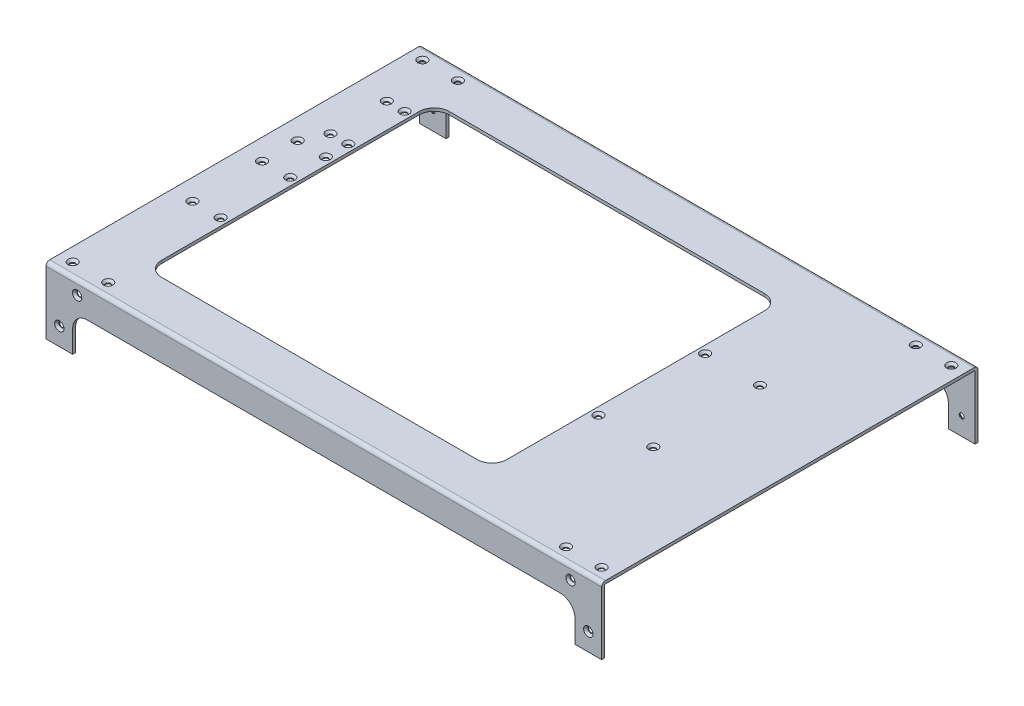
SolidWorks part; units mm, degrees
material "6061-T6 (SS)"
ref_plane "Front Plane" through (0, 0, 0) normal (0, 0, 1) x (1, 0, 0)
ref_plane "Top Plane" through (0, 0, 0) normal (0, 1, 0) x (1, 0, 0)
ref_plane "Right Plane" through (0, 0, 0) normal (1, 0, 0) x (0, 0, -1)
sketch "Sketch1" plane through (0, 0, 0) normal (1, 0, 0) x (0, 0, -1)
  line L0 (125, -45) -> (127, -45)
  line L1 (-124.5, 0) -> (124.5, 0)
  line L2 (-127, -2.5) -> (-127, -45)
  line L3 (-127, -45) -> (-125, -45)
  line L4 (127, -2.5) -> (127, -45)
  line L6 (-125, -45) -> (-125, -2.5)
  line L7 (-124.5, -2) -> (124.5, -2)
  line L8 (125, -45) -> (125, -2.5)
  arc A0 (-124.5, 0) -> (-127, -2.5) centre (-124.5, -2.5) ccw
  arc A1 (124.5, 0) -> (127, -2.5) centre (124.5, -2.5) cw
  arc A2 (124.5, -2) -> (125, -2.5) centre (124.5, -2.5) cw
  arc A3 (-125, -2.5) -> (-124.5, -2) centre (-124.5, -2.5) cw
  dimension "D1" = 2.5
  dimension "D2" = 250
  dimension "D3" = 2
  dimension "D4" = 45
extrude "Boss-Extrude1" add sketch "Sketch1" along normal mid plane 375
sketch "Sketch2" plane through (0, 0, 127) normal (0, 0, 1) x (1, 0, 0)
  line L0 (187.5, -45) -> (-187.5, -45) construction
  line L1 (-169.5, -45) -> (169.5, -45)
  line L2 (-169.5, -45) -> (-169.5, -30)
  line L3 (-159.5, -20) -> (159.5, -20)
  line L4 (169.5, -45) -> (169.5, -30)
  line L5 (-187.5, -2.5) -> (-187.5, -45) construction
  line L6 (187.5, 0) -> (-187.5, 0) construction
  line L7 (187.5, -2.5) -> (187.5, -45) construction
  arc A0 (159.5, -20) -> (169.5, -30) centre (159.5, -30) cw
  arc A1 (-169.5, -30) -> (-159.5, -20) centre (-159.5, -30) cw
  dimension "D4" = 10
  dimension "D1" = 18
  dimension "D2" = 20
  dimension "D3" = 18
extrude "Cut-Extrude1" cut sketch "Sketch2" against normal through all
sketch "Sketch3" plane through (0, 0, 0) normal (0, 1, 0) x (1, 0, 0)
  line L1 (-139.5, 97) -> (73.5, 97)
  line L2 (-149.5, 87) -> (-149.5, -87)
  line L3 (-139.5, -97) -> (73.5, -97)
  line L4 (83.5, 87) -> (83.5, -87)
  line L6 (187.5, 127) -> (-187.5, 127) construction
  line L7 (187.5, -127) -> (-187.5, -127) construction
  line L8 (187.5, 124.5) -> (187.5, -124.5) construction
  line L9 (-187.5, 124.5) -> (-187.5, -124.5) construction
  arc A0 (-149.5, -87) -> (-139.5, -97) centre (-139.5, -87) ccw
  arc A1 (73.5, -97) -> (83.5, -87) centre (73.5, -87) ccw
  arc A2 (83.5, 87) -> (73.5, 97) centre (73.5, 87) ccw
  arc A3 (-139.5, 97) -> (-149.5, 87) centre (-139.5, 87) ccw
  dimension "D5" = 10
  dimension "D1" = 30
  dimension "D2" = 30
  dimension "D3" = 104
  dimension "D4" = 38
extrude "Cut-Extrude2" cut sketch "Sketch3" against normal blind 10
sketch "Sketch4" plane through (0, 0, 127) normal (0, 0, 1) x (1, 0, 0)
  line L0 (-187.5, -2.5) -> (-187.5, -45) construction
  line L1 (187.5, 0) -> (-187.5, 0) construction
  line L2 (187.5, -2.5) -> (187.5, -45) construction
  circle A0 centre (-178.5, -33) radius 1.5
  circle A1 centre (-178.5, -9) radius 1.5 construction
  circle A2 centre (-166.5, -9) radius 1.5
  circle A3 centre (166.5, -9) radius 1.5
  circle A4 centre (178.5, -9) radius 1.5 construction
  circle A5 centre (178.5, -33) radius 1.5
  dimension "D1" = 3
  dimension "D2" = 9
  dimension "D3" = 9
  dimension "D4" = 9
  dimension "D5" = 21
  dimension "D6" = 33
  dimension "D7" = 21
extrude "Cut-Extrude3" cut sketch "Sketch4" against normal through all
sketch "Sketch5" plane through (0, 0, 0) normal (0, 1, 0) x (1, 0, 0)
  line L0 (187.5, 127) -> (-187.5, 127) construction
  line L1 (187.5, -127) -> (-187.5, -127) construction
  line L2 (-187.5, 124.5) -> (-187.5, -124.5) construction
  line L3 (187.5, 124.5) -> (187.5, -124.5) construction
  circle A0 centre (-178.5, 118) radius 1.5
  circle A1 centre (-154.5, 118) radius 1.5
  circle A2 centre (154.5, 118) radius 1.5
  circle A3 centre (178.5, 118) radius 1.5
  circle A4 centre (178.5, -118) radius 1.5
  circle A5 centre (154.5, -118) radius 1.5
  circle A6 centre (-178.5, -118) radius 1.5
  circle A7 centre (-154.5, -118) radius 1.5
  circle A8 centre (88.5, 41.85) radius 1.5
  circle A9 centre (88.5, -30.15) radius 1.5
  circle A10 centre (125.5, 41.85) radius 1.5
  circle A11 centre (125.5, -30.15) radius 1.5
  circle A12 centre (-154.5, 28.85) radius 1.5
  circle A13 centre (-173.5, 28.85) radius 1.5
  circle A14 centre (-173.5, 4.85) radius 1.5
  circle A15 centre (-154.5, 4.85) radius 1.5
  circle A16 centre (-154.5, -42.15) radius 1.5
  circle A17 centre (-173.5, -42.15) radius 1.5
  circle A18 centre (-166.5, 82) radius 1.5
  circle A19 centre (-154.5, 82) radius 1.5
  circle A20 centre (-166.5, 44) radius 1.5
  circle A21 centre (-154.5, 44) radius 1.5
  dimension "D1" = 3
  dimension "D2" = 9
  dimension "D3" = 9
  dimension "D4" = 9
  dimension "D5" = 33
  dimension "D6" = 9
  dimension "D7" = 33
extrude "Cut-Extrude4" cut sketch "Sketch5" against normal blind 10
hole_wizard "CSK for M3 Flat Head Machine Screw1" positions "Sketch7" profile "Sketch6" countersink size "M3" standard "Ansi Metric" end condition through all
sketch "Sketch7" plane through (0, 0, 0) normal (0, 1, 0) x (-1, 0, 0)
  point P0 (154.5, 118)
  point P1 (178.5, 118)
  point P7 (154.5, 42.15)
  point P10 (173.5, 42.15)
  point P13 (154.5, -4.85)
  point P16 (173.5, -4.85)
  point P19 (173.5, -28.85)
  point P22 (154.5, -28.85)
  point P25 (154.5, -44)
  point P28 (166.5, -44)
  point P31 (166.5, -82)
  point P34 (154.5, -82)
  point P37 (178.5, -118)
  point P40 (154.5, -118)
  point P43 (-154.5, -118)
  point P46 (-178.5, -118)
  point P49 (-125.5, -41.85)
  point P52 (-88.5, -41.85)
  point P55 (-125.5, 30.15)
  point P58 (-88.5, 30.15)
  point P61 (-178.5, 118)
  point P64 (-154.5, 118)
sketch "Sketch6" plane through (-154.5, 0, 118) normal (1, 0, 0) x (0, 0, 1)
  line L0 (0, 0) -> (0, 45)
  line L1 (0, 45) -> (1.7, 45)
  line L2 (1.7, 45) -> (1.7, 1.45)
  line L3 (1.7, 1.45) -> (3.15, 0)
  line L5 (3.15, 0) -> (0, 0)
  line L6 (-1.7, 1.45) -> (-3.15, 0) construction
  line L11 (0, -6.35) -> (0, 107.95) construction
  dimension "Thru Hole Dia." = 3.4
  dimension "Thru Hole Depth" = 45
  dimension "Near C'Sink Dia." = 6.3
  dimension "Near C'Sink Angle" = 90
hole_wizard "CSK for M3 Flat Head Machine Screw2" positions "Sketch9" profile "Sketch8" countersink size "M3" standard "Ansi Metric"
sketch "Sketch9" plane through (0, 0, 127) normal (0, 0, 1) x (1, 0, 0)
  point P0 (166.5, -9)
  point P1 (178.5, -33)
  point P4 (-178.5, -33)
  point P7 (-166.5, -9)
sketch "Sketch8" plane through (166.5, -9, 127) normal (1, 0, 0) x (0, -1, 0)
  line L0 (0, 0) -> (0, 11.0215)
  line L1 (0, 11.0215) -> (1.7, 10)
  line L2 (1.7, 10) -> (1.7, 1.45)
  line L3 (1.7, 1.45) -> (3.15, 0)
  line L5 (3.15, 0) -> (0, 0)
  line L6 (-1.7, 1.45) -> (-3.15, 0) construction
  line L10 (0, 11.0215) -> (-1.7, 10) construction
  line L11 (0, -6.35) -> (0, 107.95) construction
  dimension "Hole Dia." = 3.4
  dimension "Hole Depth" = 10
  dimension "Near C'Sink Dia." = 6.3
  dimension "Near C'Sink Angle" = 90
  dimension "Drill Angle" = 118
hole_wizard "CSK for M3 Flat Head Machine Screw3" positions "Sketch11" profile "Sketch10" countersink size "M3" standard "Ansi Metric"
sketch "Sketch11" plane through (0, 0, -127) normal (0, 0, -1) x (-1, 0, 0)
  point P0 (-166.5, -9)
  point P1 (178.5, -33)
  point P4 (166.5, -9)
  point P7 (-178.5, -33)
sketch "Sketch10" plane through (166.5, -9, -127) normal (1, 0, 0) x (0, 1, 0)
  line L0 (0, 0) -> (0, 11.0215)
  line L1 (0, 11.0215) -> (1.7, 10)
  line L2 (1.7, 10) -> (1.7, 1.45)
  line L3 (1.7, 1.45) -> (3.15, 0)
  line L5 (3.15, 0) -> (0, 0)
  line L6 (-1.7, 1.45) -> (-3.15, 0) construction
  line L10 (0, 11.0215) -> (-1.7, 10) construction
  line L11 (0, -6.35) -> (0, 107.95) construction
  dimension "Hole Dia." = 3.4
  dimension "Hole Depth" = 10
  dimension "Near C'Sink Dia." = 6.3
  dimension "Near C'Sink Angle" = 90
  dimension "Drill Angle" = 118
